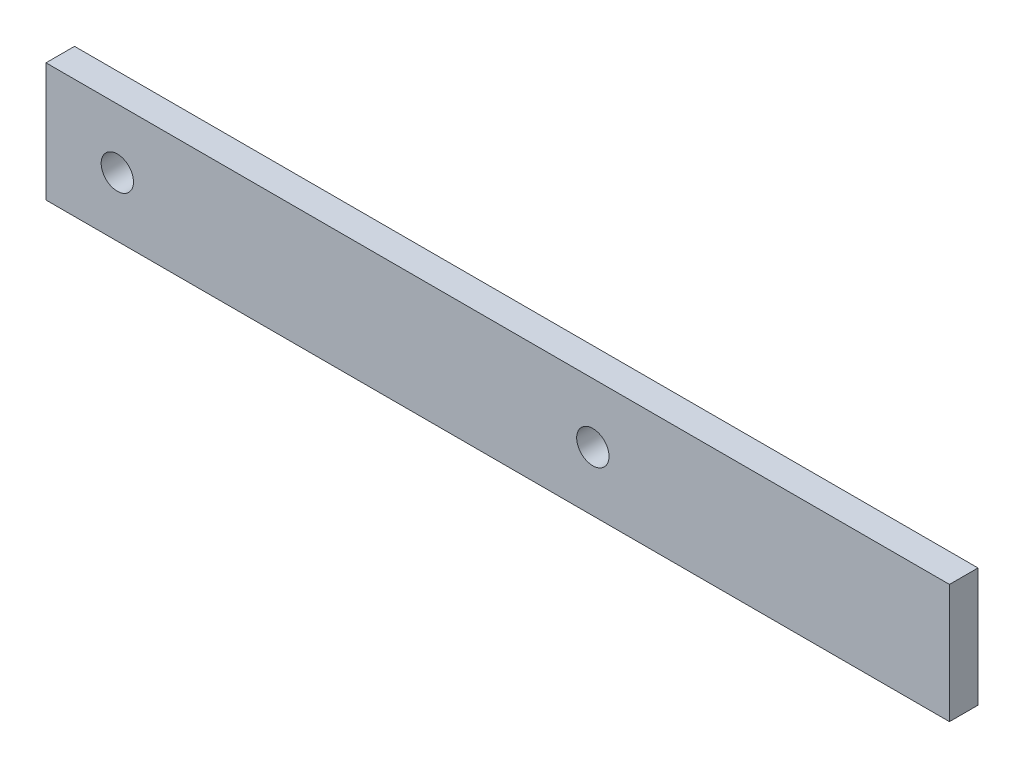
SolidWorks part; units mm, degrees
ref_plane "Front" through (0, 0, 0) normal (0, 0, 1) x (1, 0, 0)
ref_plane "Top" through (0, 0, 0) normal (0, 1, 0) x (1, 0, 0)
ref_plane "Right" through (0, 0, 0) normal (1, 0, 0) x (0, 0, -1)
sketch "Sketch1" plane through (0, 0, 0) normal (0, 0, 1) x (1, 0, 0)
  line L0 (-115, -12.5) -> (75, -12.5)
  line L1 (-115, -12.5) -> (-115, 12.5)
  line L2 (75, 12.5) -> (-115, 12.5)
  line L3 (75, 12.5) -> (75, -12.5)
  line L4 (0, 0) -> (-131.1797, 0) construction
  circle A0 centre (0, 0) radius 3.4
  circle A1 centre (-100, 0) radius 3.4
  dimension "D5" = 6.8
  dimension "D1" = 25
  dimension "D2" = 190
  dimension "D3" = 75
  dimension "D4" = 175
extrude "Base-Extrude" add sketch "Sketch1" along normal blind 6
cosmetic thread "Cosmetic Thread1" parameters "D2"=8
cosmetic thread "Cosmetic Thread2" parameters "D2"=8
cosmetic thread "Hole Thread1" parameters "D1"=6, "D2"=8
cosmetic thread "Hole Thread2" parameters "D1"=6, "D2"=8
hole_wizard "M8 Tapped Hole1" positions "3DSketch1" profile "Sketch2" tap size "M8" standard "ISO"
sketch3d "3DSketch1"
  line L0 (-100, 0, 6) -> (-100, 0, 0) construction
  line L1 (0, 0, 6) -> (0, 0, 0) construction
  point P0 (-100, 0, 6)
  point P4 (0, 0, 6)
sketch "Sketch2" plane through (-100, 0, 6) normal (1, 0, 0) x (0, -1, 0)
  line L0 (0, 0) -> (0, 24.2929)
  line L1 (0, 24.2929) -> (3.4, 22.25)
  line L2 (3.4, 22.25) -> (3.4, 0)
  line L5 (3.4, 0) -> (0, 0)
  line L10 (0, 24.2929) -> (-3.4, 22.25) construction
  line L11 (0, -6.35) -> (0, 107.95) construction
  dimension "Tap Drill Dia." = 6.8
  dimension "Tap Drill Depth" = 22.25
  dimension "Drill Angle" = 118
